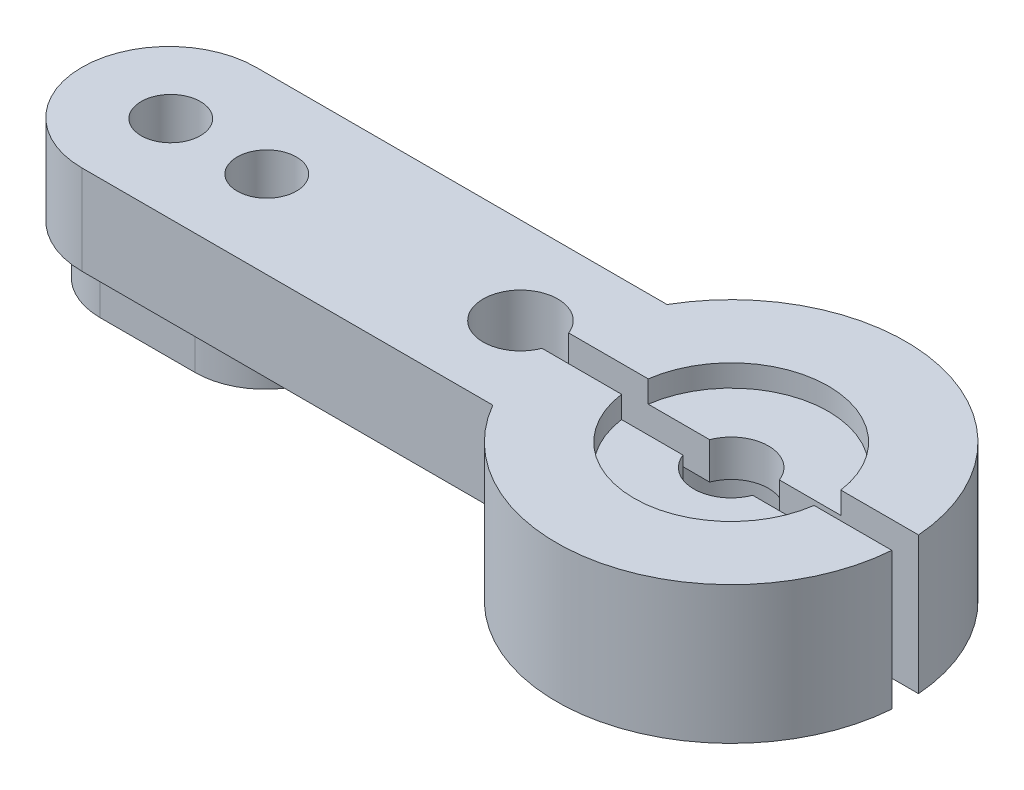
SolidWorks part; units mm, degrees
ref_plane "Front Plane" through (0, 0, 0) normal (0, 0, 1) x (1, 0, 0)
ref_plane "Top Plane" through (0, 0, 0) normal (0, 1, 0) x (1, 0, 0)
ref_plane "Right Plane" through (0, 0, 0) normal (1, 0, 0) x (0, 0, -1)
sketch "Sketch1" plane through (0, 0, 0) normal (0, 1, 0) x (1, 0, 0)
  circle A0 centre (0, 0) radius 7.4803
  dimension "D1" = 14.9606
extrude "Boss-Extrude1" add sketch "Sketch1" along normal blind 5.8928
sketch "Sketch2" plane through (0, 0, 0) normal (0, -1, 0) x (1, 0, 0)
  circle A0 centre (0, 0) radius 2.7813
  dimension "D1" = 5.5626
extrude "Cut-Extrude1" cut sketch "Sketch2" against normal blind 3.3782
sketch "Sketch4" plane through (0, 5.8928, 0) normal (0, 1, 0) x (1, 0, 0)
  line L0 (-24.0919, 3.7338) -> (-6.4818, 3.7338)
  line L1 (-24.0919, -3.7338) -> (-6.4818, -3.7338)
  arc A0 (-24.0919, 3.7338) -> (-24.0919, -3.7338) centre (-24.0919, 0) ccw
  circle A1 centre (0, 0) radius 7.4803 construction
  circle A3 centre (0, 0) radius 7.4803
  arc A4 (-6.4818, 3.7338) -> (-6.4818, -3.7338) centre (0, 0) ccw
  point P3 (-27.8257, 0)
  point P8 (-25.2194, 2.6063)
  dimension "D1" = 27.8257
  dimension "D2" = 7.4676
  dimension "D3" = 0
extrude "Boss-Extrude2" add sketch "Sketch4" against normal blind 3.8354
sketch "Sketch5" plane through (0, 2.0574, 0) normal (0, -1, 0) x (1, 0, 0)
  line L0 (-24.0284, 0) -> (-19.9644, 0) construction
  line L1 (-24.0284, 3.0099) -> (-19.9644, 3.0099)
  line L2 (-24.0284, -3.0099) -> (-19.9644, -3.0099)
  arc A0 (-24.0284, 3.0099) -> (-24.0284, -3.0099) centre (-24.0284, 0) ccw
  arc A1 (-19.9644, -3.0099) -> (-19.9644, 3.0099) centre (-19.9644, 0) ccw
  arc A2 (-24.0919, 3.7338) -> (-24.0919, -3.7338) centre (-24.0919, 0) ccw construction
  point P3 (-21.9964, 0)
  point P8 (-21.8537, 0)
  point P9 (-23.8962, 3.0099)
  point P10 (-27.0383, 0)
  point P11 (-16.9545, 0)
  point P15 (-27.8257, 0)
  dimension "D1" = 6.0198
  dimension "D2" = 10.0838
  dimension "D3" = 0.7874
extrude "Boss-Extrude3" add sketch "Sketch5" along normal blind 2.0574
sketch "Sketch6" plane through (0, 5.8928, 0) normal (0, 1, 0) x (1, 0, 0)
  circle A0 centre (0, 0) radius 4.1656
  dimension "D1" = 8.3312
extrude "Cut-Extrude2" cut sketch "Sketch6" against normal blind 0.9398
sketch "Sketch7" plane through (0, 5.8928, 0) normal (0, 1, 0) x (1, 0, 0)
  line L0 (-24.0157, 0) -> (-19.9009, 0) construction
  line L1 (-9.0297, 0.5715) -> (9.2253, 0.5715)
  line L2 (-9.0297, 0.5715) -> (-9.0297, -0.5715)
  line L3 (-9.0297, -0.5715) -> (9.2253, -0.5715)
  line L4 (9.2253, 0.5715) -> (9.2253, -0.5715)
  line L5 (-24.0157, 0) -> (-27.8257, 0) construction
  circle A0 centre (-9.0297, 0) radius 1.6002
  circle A1 centre (0, 0) radius 1.6002
  circle A2 centre (-24.0157, 0) radius 1.27
  circle A3 centre (-19.9009, 0) radius 1.27
  arc A4 (-24.0919, 3.7338) -> (-24.0919, -3.7338) centre (-24.0919, 0) ccw construction
  point P4 (9.2253, 0)
  point P6 (-9.0297, 0)
  dimension "D3" = 3.2004
  dimension "D4" = 2.54
  dimension "D5" = 4.1148
  dimension "D1" = 1.143
  dimension "D2" = 9.0297
  dimension "D6" = 3.81
extrude "Cut-Extrude3" cut sketch "Sketch7" against normal through all contours A2 | A3 | A0 | L1 L4 L3 L2 | A1
